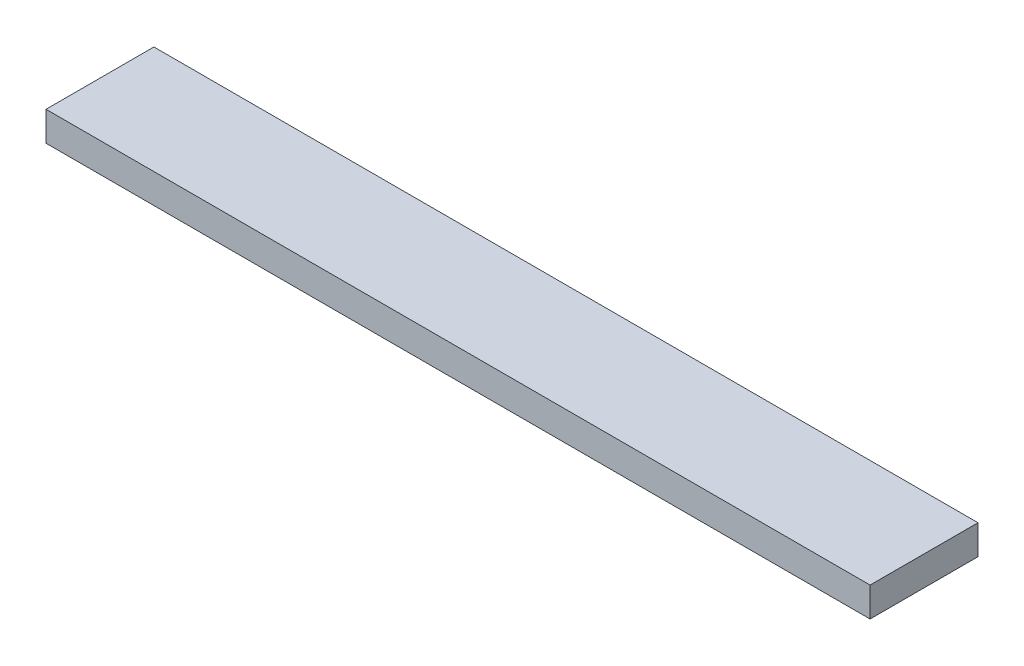
SolidWorks part; units mm, degrees
ref_plane "Front Plane" through (0, 0, 0) normal (0, 0, 1) x (1, 0, 0)
ref_plane "Top Plane" through (0, 0, 0) normal (0, 1, 0) x (1, 0, 0)
ref_plane "Right Plane" through (0, 0, 0) normal (1, 0, 0) x (0, 0, -1)
sketch "Sketch1" plane through (0, 0, 0) normal (0, 1, 0) x (1, 0, 0)
  line L1 (0, 0) -> (1066.8, 0)
  line L2 (0, 0) -> (0, 139.7)
  line L3 (0, 139.7) -> (1066.8, 139.7)
  line L4 (1066.8, 0) -> (1066.8, 139.7)
  dimension "D1" = 139.7
  dimension "D2" = 1066.8
extrude "Boss-Extrude1" add sketch "Sketch1" along normal blind 38.1
